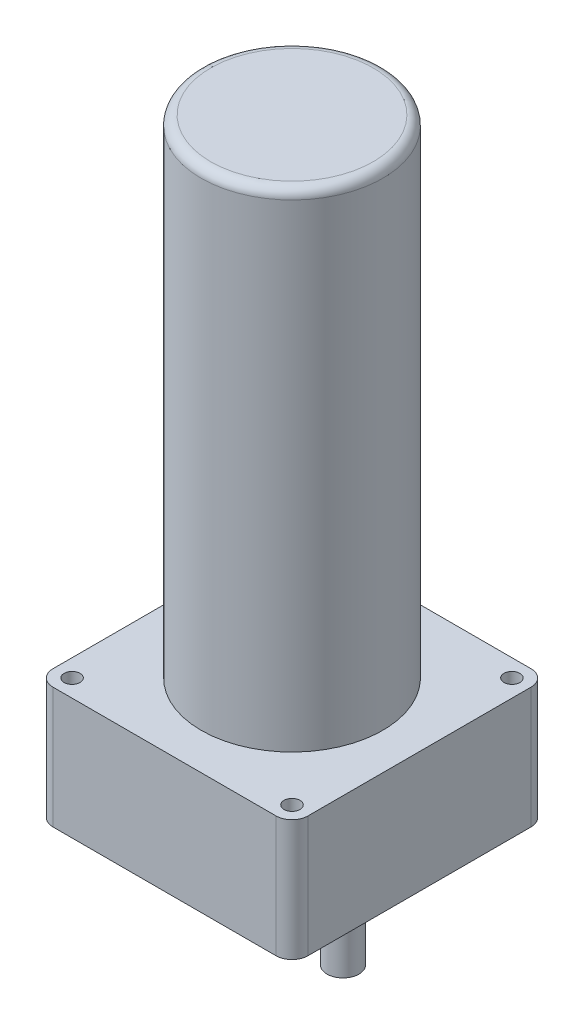
SolidWorks part; units mm, degrees
ref_plane "Front Plane" through (0, 0, 0) normal (0, 0, 1) x (1, 0, 0)
ref_plane "Top Plane" through (0, 0, 0) normal (0, 1, 0) x (1, 0, 0)
ref_plane "Right Plane" through (0, 0, 0) normal (1, 0, 0) x (0, 0, -1)
sketch "Sketch1" plane through (0, 0, 0) normal (0, 1, 0) x (1, 0, 0)
  line L1 (-40, -40) -> (40, -40)
  line L2 (-40, -40) -> (-40, 40)
  line L3 (-40, 40) -> (40, 40)
  line L4 (40, -40) -> (40, 40)
  line L5 (-40, -40) -> (40, 40) construction
  line L6 (-40, 40) -> (40, -40) construction
  point P0 (0, 0)
  dimension "D1" = 80
  dimension "D2" = 80
extrude "Boss-Extrude1" add sketch "Sketch1" along normal blind 38
sketch "Sketch2" plane through (0, 38, 0) normal (0, 1, 0) x (1, 0, 0)
  circle A0 centre (0, 0) radius 28.5
  dimension "D1" = 57
extrude "Boss-Extrude2" add sketch "Sketch2" along normal blind 153
sketch "Sketch3" plane through (0, 0, 0) normal (0, -1, 0) x (1, 0, 0)
  circle A0 centre (0, 0) radius 36.5
  dimension "D1" = 73
extrude "Cut-Extrude1" cut sketch "Sketch3" against normal blind 1
sketch "Sketch4" plane through (0, 1, 0) normal (0, -1, 0) x (1, 0, 0)
  line L0 (40, 40) -> (40, -40) construction
  circle A0 centre (16, 0) radius 15
  dimension "D1" = 30
  dimension "D2" = 24
extrude "Boss-Extrude3" add sketch "Sketch4" along normal blind 4 contours A0
sketch "Sketch5" plane through (0, -3, 0) normal (0, -1, 0) x (1, 0, 0)
  circle A0 centre (16, 0) radius 5
  dimension "D1" = 10
extrude "Boss-Extrude4" add sketch "Sketch5" along normal blind 29
fillet "Fillet1" radius 5 4 edges at (-40, 19, -40) (40, 19, -40) (40, 19, 40) (-40, 19, 40)
sketch "Sketch6" plane through (0, 0, 0) normal (0, -1, 0) x (1, 0, 0)
  line L0 (-35, 40) -> (35, 40) construction
  line L1 (-40, -35) -> (-40, 35) construction
  circle A0 centre (-34.5, 34.5) radius 2.5
  dimension "D1" = 5
  dimension "D2" = 5.5
  dimension "D3" = 5.5
extrude "Cut-Extrude2" cut sketch "Sketch6" against normal blind 38
sketch "Sketch7" plane through (0, 0, 0) normal (0, -1, 0) x (1, 0, 0)
  line L0 (-35, 40) -> (35, 40) construction
  line L1 (40, 35) -> (40, -35) construction
  line L2 (35, -40) -> (-35, -40) construction
  line L3 (-40, -35) -> (-40, 35) construction
  circle A0 centre (34.5, 34.5) radius 2.5
  circle A1 centre (34.5, -34.5) radius 2.5
  circle A2 centre (-34.5, -34.5) radius 2.5
  dimension "D1" = 5
  dimension "D2" = 5
  dimension "D3" = 5
  dimension "D4" = 5.5
  dimension "D5" = 5.5
  dimension "D6" = 5.5
  dimension "D7" = 5.5
  dimension "D8" = 5.5
  dimension "D9" = 5.5
extrude "Cut-Extrude3" cut sketch "Sketch7" against normal blind 38
fillet "Fillet2" radius 3 1 edges at (0, 191, 28.5)
